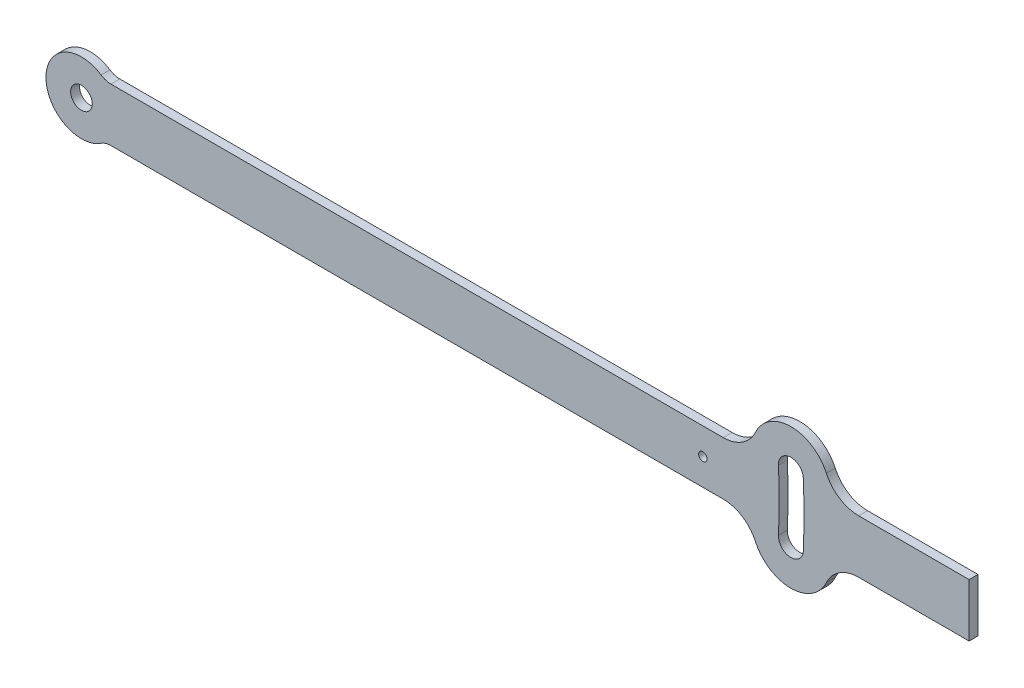
SolidWorks part; units mm, degrees
material "AISI 1020"
ref_plane "Plan de face" through (0, 0, 0) normal (0, 0, 1) x (1, 0, 0)
ref_plane "Plan de dessus" through (0, 0, 0) normal (0, 1, 0) x (1, 0, 0)
ref_plane "Plan de droite" through (0, 0, 0) normal (1, 0, 0) x (0, 0, -1)
sketch "Esquisse1" plane through (0, 0, 0) normal (0, 0, 1) x (1, 0, 0)
  line L0 (0, 0) -> (500, 0) construction
  line L1 (399.6193, 17.4478) -> (0, 0) construction
  line L2 (399.6193, -17.4478) -> (0, 0) construction
  line L3 (13.2288, 15) -> (377.7023, 15)
  line L4 (13.2288, -15) -> (377.7023, -15)
  line L5 (500, 15) -> (421.7333, 15)
  line L6 (500, -15) -> (421.7333, -15)
  line L7 (500, 15) -> (500, -15)
  line L8 (377.7023, 15) -> (421.7333, 15) construction
  line L9 (377.7023, -15) -> (421.7333, -15) construction
  circle A0 centre (0, 0) radius 6.1
  arc A1 (13.2288, 15) -> (13.2288, -15) centre (0, 0) ccw
  arc A2 (392.626, -17.1424) -> (392.626, 17.1424) centre (0, 0) ccw
  arc A3 (399.2528, -24.4382) -> (399.6193, 17.4478) centre (0, 0) ccw construction
  arc A4 (406.6126, -17.7531) -> (406.6126, 17.7531) centre (0, 0) ccw
  arc A5 (406.6126, 17.7531) -> (392.626, 17.1424) centre (399.6193, 17.4478) ccw
  arc A6 (392.626, -17.1424) -> (406.6126, -17.7531) centre (399.6193, -17.4478) ccw
  arc A7 (377.6402, -16.4881) -> (377.7023, -15) centre (0, 0) ccw
  arc A8 (421.5983, 18.4074) -> (377.6402, 16.4881) centre (399.6193, 17.4478) ccw
  arc A9 (421.5983, -18.4074) -> (421.7333, -15) centre (0, 0) ccw
  arc A10 (377.6402, -16.4881) -> (421.5983, -18.4074) centre (399.6193, -17.4478) ccw
  arc A11 (377.7023, 15) -> (377.6402, 16.4881) centre (0, 0) ccw
  arc A12 (377.6402, -16.4881) -> (377.6402, 16.4881) centre (0, 0) ccw construction
  arc A13 (421.7333, 15) -> (421.5983, 18.4074) centre (0, 0) ccw
  arc A14 (421.5983, -18.4074) -> (421.5983, 18.4074) centre (0, 0) ccw construction
  circle A15 centre (350, 0) radius 2.4
  point P31 (400, 0)
  dimension "D3" = 12.2
  dimension "D6" = 14
  dimension "D7" = 400
  dimension "D9" = 40
  dimension "D11" = 4.8
  dimension "D4" = 15
  dimension "D1" = 2.5
  dimension "D2" = 2.5
  dimension "D5" = 30
  dimension "D8" = 500
  dimension "D10" = 50
extrude "Boss.-Extru.1" add sketch "Esquisse1" along normal blind 5
fillet "Congé1" radius 10 2 edges at (13.2288, -15, 2.5) (13.2288, 15, 2.5)
fillet "Congé2" radius 20 4 edges at (421.7333, 15, 2.5) (421.7333, -15, 2.5) (377.7023, 15, 2.5) (377.7023, -15, 2.5)
